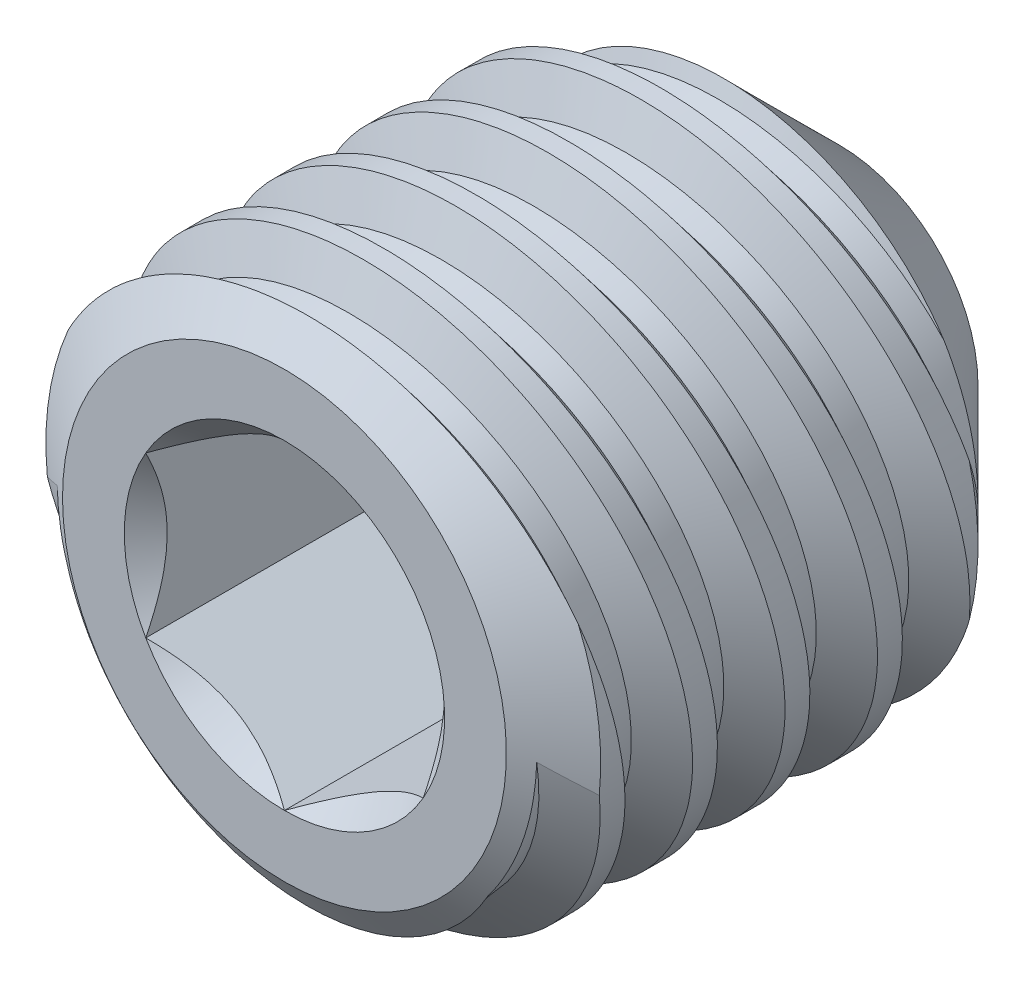
SolidWorks part; units mm, degrees
ref_plane "Front" through (0, 0, 0) normal (0, 0, 1) x (1, 0, 0)
ref_plane "Top" through (0, 0, 0) normal (0, 1, 0) x (1, 0, 0)
ref_plane "Right" through (0, 0, 0) normal (1, 0, 0) x (0, 0, -1)
sketch "Sketch22" plane through (0, 0, 0) normal (1, 0, 0) x (0, 0, -1)
  line L0 (-1.2747, 0) -> (-1.2747, 1.2)
  line L1 (-1.2747, 1.2) -> (-1.0646, 1.5)
  line L2 (-1.0646, 1.5) -> (0.9753, 1.5)
  line L3 (0.9753, 1.5) -> (1.7253, 0.75)
  line L4 (1.7253, 0.75) -> (1.2747, 0)
  line L5 (1.2747, 0) -> (-1.2747, 0)
  line L6 (1.2747, 0) -> (1.7253, 0) construction
  line L7 (1.7253, 0) -> (1.7253, 0.75) construction
  line L8 (1.7253, -0.75) -> (1.2747, 0) construction
  line L9 (-1.0646, -1.5) -> (0.9753, -1.5) construction
  dimension "Screw Dia" = 3
  dimension "Length" = 3
  dimension "D3" = 35
  dimension "Cup Point Dia" = 1.5
  dimension "D5" = 118
  dimension "D6" = 45
  dimension "D7" = 2.4
revolve "Revolve1" add sketch "Sketch22" angle 360 about L6
sketch "Sketch6" plane through (0, 0, 0) normal (1, 0, 0) x (0, 0, -1)
  line L0 (0.1902, 1.5) -> (0.6902, -1.5) construction
  line L1 (-1.0646, 1.5) -> (0.9753, 1.5) construction
  line L2 (-1.0646, -1.5) -> (0.9753, -1.5) construction
  line L3 (0.1902, 1.5) -> (0.2518, 1.5103) construction
  line L4 (0.5738, 1.2896) -> (0.4505, 1.269)
  line L5 (0.4505, 1.269) -> (0.2518, 1.5103)
  line L6 (0.5738, 1.2896) -> (0.6834, 1.5822)
  line L7 (0.6834, 1.5822) -> (0.2518, 1.5103)
  line L8 (0.4753, 1.5) -> (0.9753, -1.5) construction
  line L9 (1.2605, 0.0892) -> (0.1902, -0.0892) construction
  line L10 (0.4676, 1.5462) -> (0.5121, 1.2793) construction
  line L13 (0.1902, -1.5) -> (0.1902, 1.5) construction
  line L14 (0.1902, -1.5) -> (0.6902, -1.5) construction
  line L15 (0.6902, -1.5) -> (0.9753, -1.5) construction
  line L18 (0.1902, 1.5) -> (0.4753, 1.5) construction
  point P18 (0.7253, 0)
  dimension "D1" = 0.5
  dimension "D2" = 0.125
  dimension "D3" = 60
  dimension "D4" = 0.0625
  dimension "Pitch" = 0.5
revolve "Cut-Revolve8" cut sketch "Sketch6" angle 360 about L9
pattern_linear "LPattern1" count 5 spacing 0.5 along (0, 0, 1) count 2 spacing 0.5 along (0, 0, -1) of "Cut-Revolve8"
sketch "Sketch23" plane through (0, 0, 1.2747) normal (0, 0, 1) x (1, 0, 0)
  line L1 (0, 0.866) -> (-0.75, 0.433)
  line L2 (-0.75, 0.433) -> (-0.75, -0.433)
  line L3 (-0.75, -0.433) -> (0, -0.866)
  line L4 (0, -0.866) -> (0.75, -0.433)
  line L5 (0.75, -0.433) -> (0.75, 0.433)
  line L6 (0.75, 0.433) -> (0, 0.866)
  circle A0 centre (0, 0) radius 0.75 construction
  dimension "Hex" = 1.5
extrude "Cut-Extrude10" cut sketch "Sketch23" against normal blind 1.5
sketch "Sketch24" plane through (0, 0, 1.2747) normal (0, 0, 1) x (1, 0, 0)
  circle A0 centre (0, 0) radius 0.866
extrude "Cut-Extrude11" cut sketch "Sketch24" against normal through all draft 45
sketch "Sketch26" plane through (0, 0, -0.2253) normal (0, 0, 1) x (1, 0, 0)
  circle A0 centre (0, 0) radius 0.75 construction
  circle A1 centre (0, 0) radius 0.75
extrude "Cut-Extrude12" cut sketch "Sketch26" against normal through all draft 59
equation "\"D2@Sketch6\"=\"Pitch@Sketch6\"/4"
equation "\"D4@Sketch6\"=\"Pitch@Sketch6\"/8"
equation "\"D1@Sketch6\"=\"Pitch@Sketch6\""
equation "\"D3@LPattern1\"=\"Pitch@Sketch6\""
equation "\"D1@LPattern1\"=(\"Length@Sketch22\"/\"Pitch@Sketch6\")-1"
equation "\"D4@LPattern1\"=\"Pitch@Sketch6\""
equation "\"D7@Sketch22\"=\"Screw Dia@Sketch22\"*.8"
